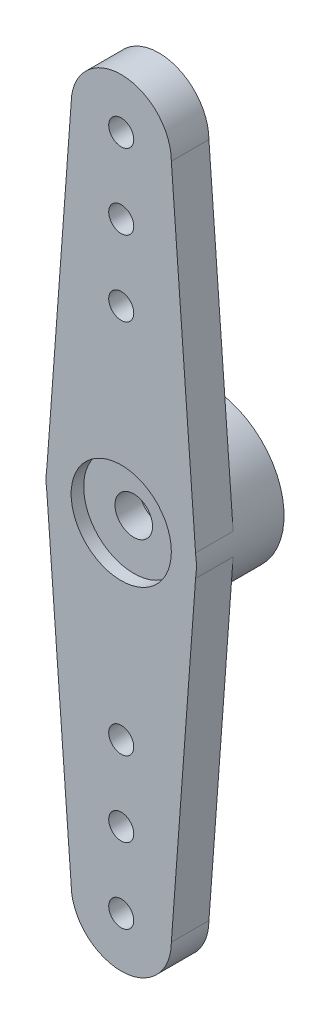
SolidWorks part; units mm, degrees
material "PLA"
ref_plane "Plan de face" through (0, 0, 0) normal (0, 0, 1) x (1, 0, 0)
ref_plane "Plan de dessus" through (0, 0, 0) normal (0, 1, 0) x (1, 0, 0)
ref_plane "Plan de droite" through (0, 0, 0) normal (1, 0, 0) x (0, 0, -1)
sketch "Esquisse1" plane through (0, 0, 0) normal (0, 0, 1) x (1, 0, 0)
  line L0 (0, 0) -> (0, 15.5) construction
  line L1 (2, 13.5) -> (2.9673, 0.442)
  line L2 (-2, 13.5) -> (-2.9673, 0.442)
  line L3 (-15.6661, 0) -> (13.91, 0) construction
  line L4 (2, -13.5) -> (2.9673, -0.442)
  line L5 (-2, -13.5) -> (-2.9673, -0.442)
  arc A0 (-2.9673, 0.442) -> (-2.9673, -0.442) centre (0, 0) ccw
  arc A1 (2, 13.5) -> (-2, 13.5) centre (0, 13.5) ccw
  arc A2 (2, -13.5) -> (-2, -13.5) centre (0, -13.5) cw
  arc A3 (2.9673, -0.442) -> (2.9673, 0.442) centre (0, 0) ccw
  dimension "D1" = 6
  dimension "D2" = 4
  dimension "D3" = 13.5
  dimension "D4" = 13.058
  dimension "D5" = 13.058
  dimension "D6" = 13.058
  dimension "D7" = 13.058
extrude "Boss.-Extru.2" add sketch "Esquisse1" along normal blind 1.5
sketch "Esquisse2" plane through (0, 0, 0) normal (0, 0, -1) x (-1, 0, 0)
  circle A0 centre (0, 0) radius 3
  circle A1 centre (0, 0) radius 2
  dimension "D1" = 6
  dimension "D2" = 1
extrude "Boss.-Extru.3" add sketch "Esquisse2" along normal blind 2
sketch "Esquisse3" plane through (0, 0, 0) normal (0, 0, -1) x (-1, 0, 0)
  circle A0 centre (0, 0) radius 0.75
  dimension "D1" = 1.5
extrude "Enlèv. mat.-Extru.1" cut sketch "Esquisse3" against normal blind 2
sketch "Esquisse4" plane through (0, 0, 1.5) normal (0, 0, 1) x (1, 0, 0)
  circle A0 centre (0, 0) radius 2
  dimension "D1" = 4
extrude "Enlèv. mat.-Extru.2" cut sketch "Esquisse4" against normal blind 0.5
sketch "Esquisse5" plane through (0, 0, 1.5) normal (0, 0, 1) x (1, 0, 0)
  line L0 (0, -16.2626) -> (0, 16.9239) construction
  circle A0 centre (0, 13.5) radius 0.5
  dimension "D1" = 1
extrude "Enlèv. mat.-Extru.3" cut sketch "Esquisse5" against normal through all
pattern_linear "Répétition linéaire1" count 3 spacing 3 along (0, -1, 0) of "Enlèv. mat.-Extru.3"
mirror "Symétrie1" about plane through (0, 0, 0) normal (0, 1, 0) of "Répétition linéaire1", "Enlèv. mat.-Extru.3"
